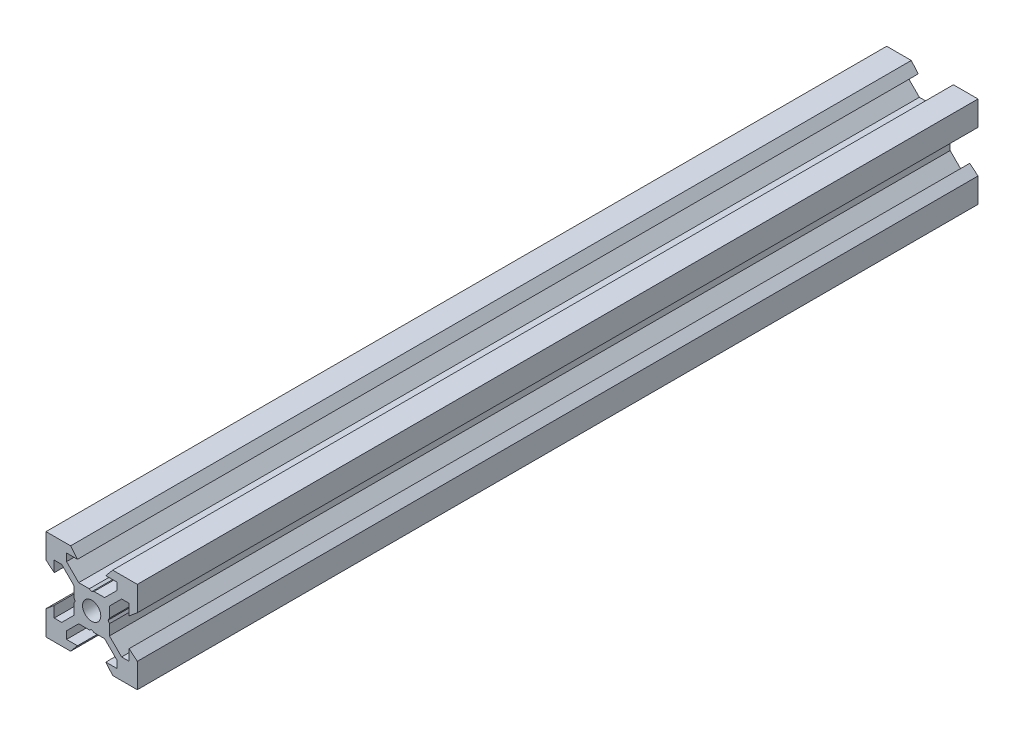
SolidWorks part; units mm, degrees
ref_plane "Front Plane" through (0, 0, 0) normal (0, 0, 1) x (1, 0, 0)
ref_plane "Top Plane" through (0, 0, 0) normal (0, 1, 0) x (1, 0, 0)
ref_plane "Right Plane" through (0, 0, 0) normal (1, 0, 0) x (0, 0, -1)
sketch "Sketch1" plane through (0, 0, 0) normal (0, 0, 1) x (1, 0, 0)
  line L0 (10, 10) -> (4.6104, 10) construction
  line L1 (10, 10) -> (10, 4.6104) construction
  line L2 (10, -10) -> (10, -4.6104) construction
  line L3 (10, -10) -> (4.6104, -10) construction
  line L4 (10, 10) -> (10, 4.6104)
  line L5 (6.5607, 5.5) -> (8.2, 5.5)
  line L6 (5.5, 8.2) -> (5.5, 6.5607)
  line L7 (10, 10) -> (4.6104, 10)
  line L8 (10, 10) -> (10, 4.6104)
  line L9 (6.5607, 5.5) -> (3.9, 2.8393)
  line L10 (5.5, 6.5607) -> (2.8393, 3.9)
  line L11 (10, 4.6104) -> (8.2, 3.1)
  line L12 (4.6104, 10) -> (3.1, 8.2)
  line L13 (8.2, 3.1) -> (8.2, 5.5)
  line L14 (3.1, 8.2) -> (5.5, 8.2)
  line L15 (-6.5607, 5.5) -> (-8.2, 5.5)
  line L16 (6.5607, -5.5) -> (8.2, -5.5)
  line L17 (3.1, -8.2) -> (5.5, -8.2)
  line L18 (8.2, -3.1) -> (8.2, -5.5)
  line L19 (4.6104, -10) -> (3.1, -8.2)
  line L20 (10, -4.6104) -> (8.2, -3.1)
  line L21 (0.5196, -3.9) -> (0, -3.6)
  line L22 (0.5196, 3.9) -> (0, 3.6)
  line L23 (3.6, 0) -> (3.9, -0.5196)
  line L24 (3.9, 0.5196) -> (3.6, 0)
  line L25 (3.9, 0.5196) -> (3.9, 2.8393)
  line L26 (2.8393, 3.9) -> (0.5196, 3.9)
  line L27 (3.9, -2.8393) -> (3.9, -0.5196)
  line L28 (2.8393, -3.9) -> (0.5196, -3.9)
  line L29 (5.5, -6.5607) -> (2.8393, -3.9)
  line L30 (6.5607, -5.5) -> (3.9, -2.8393)
  line L31 (10, -10) -> (10, -4.6104)
  line L32 (10, -10) -> (4.6104, -10)
  line L33 (5.5, -8.2) -> (5.5, -6.5607)
  line L34 (-6.5607, -5.5) -> (-8.2, -5.5)
  line L35 (10, -10) -> (10, -4.6104)
  line L36 (0, 0) -> (0, 8.2) construction
  line L37 (-10, -10) -> (-4.6104, -10) construction
  line L38 (-10, -10) -> (-10, -4.6104) construction
  line L39 (-10, 10) -> (-10, 4.6104) construction
  line L40 (-10, 10) -> (-4.6104, 10) construction
  line L41 (-10, -10) -> (-10, -4.6104)
  line L43 (-5.5, -8.2) -> (-5.5, -6.5607)
  line L44 (-10, -10) -> (-4.6104, -10)
  line L45 (-10, -10) -> (-10, -4.6104)
  line L46 (-6.5607, -5.5) -> (-3.9, -2.8393)
  line L47 (-5.5, -6.5607) -> (-2.8393, -3.9)
  line L48 (-2.8393, -3.9) -> (-0.5196, -3.9)
  line L49 (-3.9, -2.8393) -> (-3.9, -0.5196)
  line L50 (-2.8393, 3.9) -> (-0.5196, 3.9)
  line L51 (-3.9, 0.5196) -> (-3.9, 2.8393)
  line L52 (-3.9, 0.5196) -> (-3.6, 0)
  line L53 (-3.6, 0) -> (-3.9, -0.5196)
  line L54 (-0.5196, 3.9) -> (0, 3.6)
  line L55 (-0.5196, -3.9) -> (0, -3.6)
  line L56 (-10, -4.6104) -> (-8.2, -3.1)
  line L57 (-4.6104, -10) -> (-3.1, -8.2)
  line L58 (-8.2, -3.1) -> (-8.2, -5.5)
  line L59 (-3.1, -8.2) -> (-5.5, -8.2)
  line L60 (-10, -10) -> (10, -10) construction
  line L61 (-10, -10) -> (-10, 10) construction
  line L62 (-3.1, 8.2) -> (-5.5, 8.2)
  line L63 (-8.2, 3.1) -> (-8.2, 5.5)
  line L64 (-4.6104, 10) -> (-3.1, 8.2)
  line L65 (-10, 4.6104) -> (-8.2, 3.1)
  line L66 (-5.5, 6.5607) -> (-2.8393, 3.9)
  line L67 (-6.5607, 5.5) -> (-3.9, 2.8393)
  line L68 (-10, 10) -> (-10, 4.6104)
  line L69 (-10, 10) -> (-4.6104, 10)
  line L70 (-5.5, 8.2) -> (-5.5, 6.5607)
  line L71 (-10, 10) -> (10, 10) construction
  line L72 (-10, 10) -> (-10, 4.6104)
  line L73 (10, -10) -> (10, 10) construction
  line L74 (-10, -10) -> (10, 10) construction
  line L75 (-10, 10) -> (10, -10) construction
  circle A0 centre (0, 0) radius 2
  dimension "D7" = 4
  dimension "D1" = 20
  dimension "D2" = 5.3896
  dimension "D3" = 4.5
  dimension "D4" = 50
  dimension "D5" = 1.8
  dimension "D6" = 1.5104
  dimension "D8" = 5.5
  dimension "D9" = 120
  dimension "D10" = 0.3
  dimension "D11" = 2.3197
  dimension "D12" = 7.8
  dimension "D13" = 7.8
  dimension "D14" = 1.5
  dimension "D15" = 2.6607
extrude "Boss-Extrude1" add sketch "Sketch1" along normal mid plane 184.15 contours L70 L62 L64 L69 L68 L65 L63 L15 L67 L51 L52 L53 L49 L46 L34 L58 L56 L41 L44 L57 L59 L43 L47 L48 L55 L21 L28 L29 L33 L17 L19 L32 L31 L20 L18 L16 L30 L27 L23 L24 L25 L9 L5 L13 L11 L4 L7 L12 L14 L6 L10
